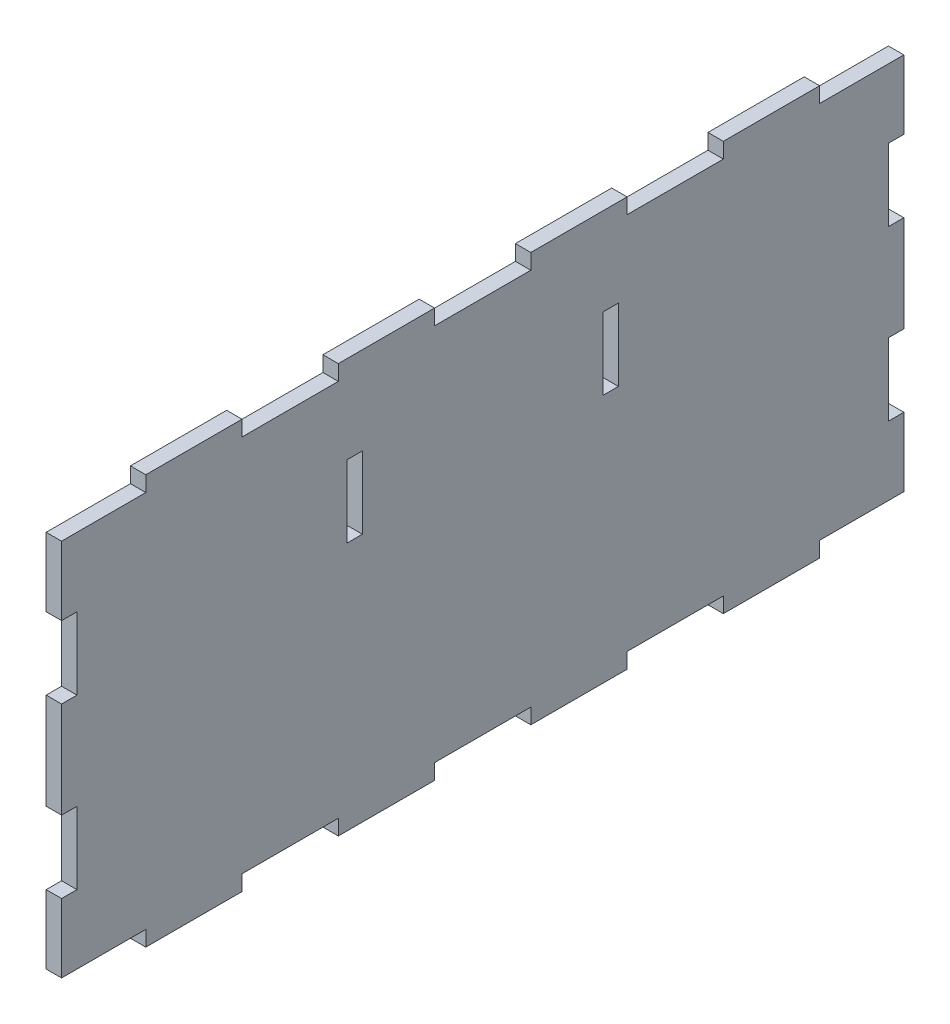
SolidWorks part; units mm, degrees
ref_plane "Front Plane" through (0, 0, 0) normal (0, 0, 1) x (1, 0, 0)
ref_plane "Top Plane" through (0, 0, 0) normal (0, 1, 0) x (1, 0, 0)
ref_plane "Right Plane" through (0, 0, 0) normal (1, 0, 0) x (0, 0, -1)
sketch "Sketch1" plane through (0, 0, 0) normal (1, 0, 0) x (0, 0, -1)
  line L0 (-10, 42.5) -> (-30, 42.5)
  line L1 (0, 55) -> (0, -55) construction
  line L2 (-87.5, 39.3) -> (-87.5, 25)
  line L3 (55, 0) -> (-55, 0) construction
  line L4 (0, 0) -> (-87.5, 0) construction
  line L5 (-87.5, 10) -> (-84.3, 10)
  line L6 (-84.3, 10) -> (-84.3, 25)
  line L7 (-84.3, 25) -> (-87.5, 25)
  line L8 (-87.5, 10) -> (-87.5, -10)
  line L9 (-87.5, 39.3) -> (-70, 39.3)
  line L10 (-70, 39.3) -> (-70, 42.5)
  line L11 (-50, 42.5) -> (-50, 39.3)
  line L12 (-50, 39.3) -> (-30, 39.3)
  line L13 (-30, 39.3) -> (-30, 42.5)
  line L14 (-10, 42.5) -> (-10, 39.3)
  line L15 (-10, 39.3) -> (10, 39.3)
  line L16 (-50, 42.5) -> (-70, 42.5)
  line L17 (0, 0) -> (0, 39.3) construction
  line L18 (-10, -39.3) -> (10, -39.3)
  line L19 (-50, -42.5) -> (-70, -42.5)
  line L20 (-10, -42.5) -> (-10, -39.3)
  line L21 (-30, -39.3) -> (-30, -42.5)
  line L22 (-50, -39.3) -> (-30, -39.3)
  line L23 (-50, -42.5) -> (-50, -39.3)
  line L24 (-70, -39.3) -> (-70, -42.5)
  line L25 (-87.5, -39.3) -> (-70, -39.3)
  line L26 (-84.3, -25) -> (-87.5, -25)
  line L27 (-84.3, -10) -> (-84.3, -25)
  line L28 (-87.5, -10) -> (-84.3, -10)
  line L29 (-87.5, -39.3) -> (-87.5, -25)
  line L30 (-10, -42.5) -> (-30, -42.5)
  line L31 (10, -42.5) -> (30, -42.5)
  line L32 (87.5, -39.3) -> (87.5, -25)
  line L33 (87.5, -10) -> (84.3, -10)
  line L34 (84.3, -10) -> (84.3, -25)
  line L35 (84.3, -25) -> (87.5, -25)
  line L36 (87.5, -39.3) -> (70, -39.3)
  line L37 (70, -39.3) -> (70, -42.5)
  line L38 (50, -42.5) -> (50, -39.3)
  line L39 (50, -39.3) -> (30, -39.3)
  line L40 (30, -39.3) -> (30, -42.5)
  line L41 (10, -42.5) -> (10, -39.3)
  line L42 (50, -42.5) -> (70, -42.5)
  line L43 (50, 42.5) -> (70, 42.5)
  line L44 (10, 42.5) -> (10, 39.3)
  line L45 (30, 39.3) -> (30, 42.5)
  line L46 (50, 39.3) -> (30, 39.3)
  line L47 (50, 42.5) -> (50, 39.3)
  line L48 (70, 39.3) -> (70, 42.5)
  line L49 (87.5, 39.3) -> (70, 39.3)
  line L50 (87.5, 10) -> (87.5, -10)
  line L51 (84.3, 25) -> (87.5, 25)
  line L52 (84.3, 10) -> (84.3, 25)
  line L53 (87.5, 10) -> (84.3, 10)
  line L54 (87.5, 39.3) -> (87.5, 25)
  line L55 (10, 42.5) -> (30, 42.5)
  line L56 (-25, 9.3) -> (-25, 24.3)
  line L57 (28.2, 9.3) -> (25, 9.3)
  line L58 (28.2, 9.3) -> (28.2, 24.3)
  line L59 (28.2, 24.3) -> (25, 24.3)
  line L60 (25, 9.3) -> (25, 24.3)
  line L61 (-28.2, 24.3) -> (-25, 24.3)
  line L62 (-28.2, 9.3) -> (-28.2, 24.3)
  line L63 (-28.2, 9.3) -> (-25, 9.3)
  point P36 (0, -39.3)
  dimension "D1" = 87.5
  dimension "D2" = 10
  dimension "D3" = 3.2
  dimension "D4" = 15
  dimension "D5" = 10
  dimension "D6" = 3.2
  dimension "D7" = 20
  dimension "D8" = 20
  dimension "D9" = 20
  dimension "D10" = 42.5
  dimension "D11" = 15
  dimension "D12" = 25
  dimension "D13" = 3.2
  dimension "D14" = 15
extrude "Boss-Extrude1" add sketch "Sketch1" along normal blind 3.2
